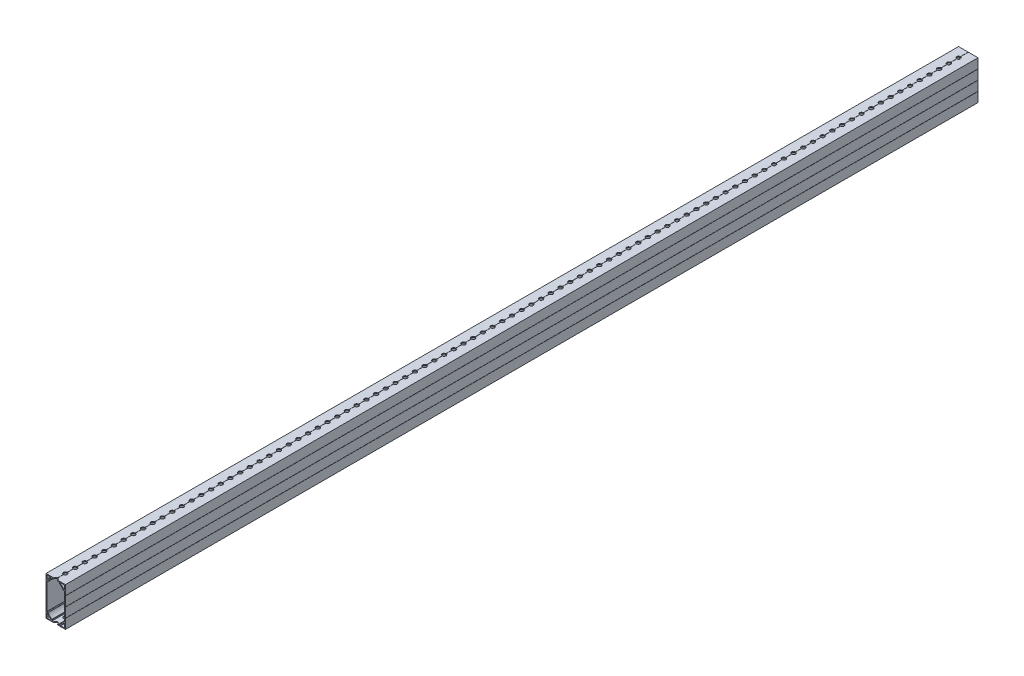
SolidWorks part; units mm, degrees
material "6061 Alloy"
ref_plane "Front Plane" through (0, 0, 0) normal (0, 0, 1) x (1, 0, 0)
ref_plane "Top Plane" through (0, 0, 0) normal (0, 1, 0) x (1, 0, 0)
ref_plane "Right Plane" through (0, 0, 0) normal (1, 0, 0) x (0, 0, -1)
other "Configuration Table"
sketch "Sketch3" plane through (0, 0, 0) normal (0, 0, 1) x (1, 0, 0)
  line L0 (0, 12.7) -> (0, -12.7) construction
  line L1 (12.7, -25.4) -> (0.127, -25.4)
  line L2 (12.7, -12.827) -> (12.7, -25.4)
  line L3 (12.573, -12.7) -> (12.7, -12.827)
  line L4 (-10.9924, -24.384) -> (-6.5971, -24.384)
  line L5 (-11.684, -19.2971) -> (-11.684, -23.6924)
  line L6 (12.7, -12.573) -> (12.573, -12.7)
  line L7 (12.7, -0.127) -> (12.7, -12.573)
  line L10 (12.573, 0) -> (12.7, -0.127)
  line L11 (0.127, -25.4) -> (0, -25.273)
  line L14 (11.684, 0) -> (11.684, -17.5895)
  line L15 (11.684, -17.5895) -> (9.979, -17.5895)
  line L18 (4.8895, -22.679) -> (4.8895, -24.384)
  line L19 (11.684, -19.2971) -> (11.684, -23.6924)
  line L20 (10.9924, -24.384) -> (6.5971, -24.384)
  line L21 (55, 0) -> (-55, 0) construction
  line L37 (12.573, 0) -> (12.7, 0.127)
  line L46 (-4.8895, -24.384) -> (4.8895, -24.384)
  line L47 (-4.8895, -22.679) -> (-4.8895, -24.384)
  line L48 (-11.684, -17.5895) -> (-9.979, -17.5895)
  line L49 (-11.684, 0) -> (-11.684, -17.5895)
  line L57 (-0.127, 25.4) -> (-12.7, 25.4)
  line L58 (-12.7, 12.827) -> (-12.7, 25.4)
  line L59 (-12.573, 12.7) -> (-12.7, 12.827)
  line L60 (-12.7, 12.573) -> (-12.573, 12.7)
  line L61 (-12.7, 0.127) -> (-12.7, 12.573)
  line L62 (-12.573, 0) -> (-12.7, 0.127)
  line L63 (-0.127, 25.4) -> (0, 25.273)
  line L64 (-11.684, 0) -> (-11.684, 17.5895)
  line L65 (-11.684, 17.5895) -> (-9.979, 17.5895)
  line L66 (-4.8895, 22.679) -> (-4.8895, 24.384)
  line L67 (-4.8895, 24.384) -> (4.8895, 24.384)
  line L69 (10.9924, 24.384) -> (6.5971, 24.384)
  line L70 (11.684, 19.2971) -> (11.684, 23.6924)
  line L71 (4.8895, 22.679) -> (4.8895, 24.384)
  line L72 (11.684, 17.5895) -> (9.979, 17.5895)
  line L73 (11.684, 0) -> (11.684, 17.5895)
  line L74 (0.127, 25.4) -> (0, 25.273)
  line L76 (12.7, 0.127) -> (12.7, 12.573)
  line L77 (12.7, 12.573) -> (12.573, 12.7)
  line L78 (-11.684, 19.2971) -> (-11.684, 23.6924)
  line L79 (-10.9924, 24.384) -> (-6.5971, 24.384)
  line L80 (12.573, 12.7) -> (12.7, 12.827)
  line L81 (12.7, 12.827) -> (12.7, 25.4)
  line L82 (12.7, 25.4) -> (0.127, 25.4)
  line L96 (-0.127, -25.4) -> (0, -25.273)
  line L118 (-12.573, 0) -> (-12.7, -0.127)
  line L119 (-12.7, -0.127) -> (-12.7, -12.573)
  line L120 (-12.7, -12.573) -> (-12.573, -12.7)
  line L121 (-12.573, -12.7) -> (-12.7, -12.827)
  line L122 (-12.7, -12.827) -> (-12.7, -25.4)
  line L123 (-12.7, -25.4) -> (-0.127, -25.4)
  arc A0 (9.979, -17.5895) -> (4.8895, -22.679) centre (0, -12.7) cw
  arc A1 (6.5971, -24.384) -> (6.2412, -23.0994) centre (6.5971, -23.6924) cw
  arc A2 (10.3994, -18.9412) -> (6.2412, -23.0994) centre (0, -12.7) cw
  arc A3 (10.3994, -18.9412) -> (11.684, -19.2971) centre (10.9924, -19.2971) cw
  arc A4 (11.684, -23.6924) -> (10.9924, -24.384) centre (10.9924, -23.6924) cw
  arc A10 (-11.684, -23.6924) -> (-10.9924, -24.384) centre (-10.9924, -23.6924) ccw
  arc A11 (-10.3994, -18.9412) -> (-11.684, -19.2971) centre (-10.9924, -19.2971) ccw
  arc A12 (-10.3994, -18.9412) -> (-6.2412, -23.0994) centre (0, -12.7) ccw
  arc A14 (-6.5971, -24.384) -> (-6.2412, -23.0994) centre (-6.5971, -23.6924) ccw
  arc A24 (-9.979, 17.5895) -> (-4.8895, 22.679) centre (0, 12.7) cw
  arc A25 (-6.5971, 24.384) -> (-6.2412, 23.0994) centre (-6.5971, 23.6924) cw
  arc A30 (-10.3994, 18.9412) -> (-6.2412, 23.0994) centre (0, 12.7) cw
  arc A31 (-10.3994, 18.9412) -> (-11.684, 19.2971) centre (-10.9924, 19.2971) cw
  arc A32 (-11.684, 23.6924) -> (-10.9924, 24.384) centre (-10.9924, 23.6924) cw
  arc A33 (11.684, 23.6924) -> (10.9924, 24.384) centre (10.9924, 23.6924) ccw
  arc A34 (10.3994, 18.9412) -> (11.684, 19.2971) centre (10.9924, 19.2971) ccw
  arc A35 (10.3994, 18.9412) -> (6.2412, 23.0994) centre (0, 12.7) ccw
  arc A41 (6.5971, 24.384) -> (6.2412, 23.0994) centre (6.5971, 23.6924) ccw
  arc A42 (9.979, 17.5895) -> (4.8895, 22.679) centre (0, 12.7) ccw
  arc A46 (-9.979, -17.5895) -> (-4.8895, -22.679) centre (0, -12.7) ccw
  point P71 (0, -24.384)
  point P104 (-11.684, -8.7948)
  point P108 (11.684, -8.7948)
  point P130 (11.684, 8.7948)
  point P131 (-11.684, 8.7948)
  point P132 (0, 24.384)
  dimension "D4" = 0.6916
  dimension "D7" = 11.1125
  dimension "D14" = 12.1285
  dimension "D1" = 25.4
  dimension "D2" = 12.573
  dimension "D3" = 5.7785
  dimension "D5" = 12.7
  dimension "D6" = 4.8895
  dimension "D8" = 1.016
  dimension "D9" = 135
  dimension "D10" = 0.127
  dimension "D11" = 1.016
  dimension "D12" = 135
  dimension "D13" = 135
extrude "Boss-Extrude1" add sketch "Sketch3" along normal blind 1193.8
sketch "Sketch2" plane through (25.4, 25.4, 0) normal (0, -1, 0) x (0, 0, 1)
  line L2 (1193.8, 25.4) -> (0, 25.4) construction
  line L3 (0, 12.7) -> (0, 25.273) construction
  circle A0 centre (12.7, 25.4) radius 2.54
  dimension "D1" = 5.08
  dimension "D2" = 12.7
extrude "Cut-Extrude1" cut sketch "Sketch2" along normal through all
pattern_linear "LPattern1" count 95 spacing 12.7 along (0, 0, 1) of "Cut-Extrude1"
fillet "Fillet1" radius 0.254 16 edges at (9.979, 17.5895, 596.9) (11.684, 17.5895, 596.9) (4.8895, 22.679, 596.9) (4.8895, 24.384, 596.9) (11.684, -17.5895, 596.9) (9.979, -17.5895, 596.9) (4.8895, -22.679, 596.9) (4.8895, -24.384, 596.9) (-4.8895, -22.679, 596.9) (-4.8895, -24.384, 596.9) (-9.979, -17.5895, 596.9) (-11.684, -17.5895, 596.9) (-4.8895, 24.384, 596.9) (-4.8895, 22.679, 596.9) (-11.684, 17.5895, 596.9) (-9.979, 17.5895, 596.9)
equation "\"Length\"= 47"
equation "\"D1@Boss-Extrude1\"=\"Length\""
